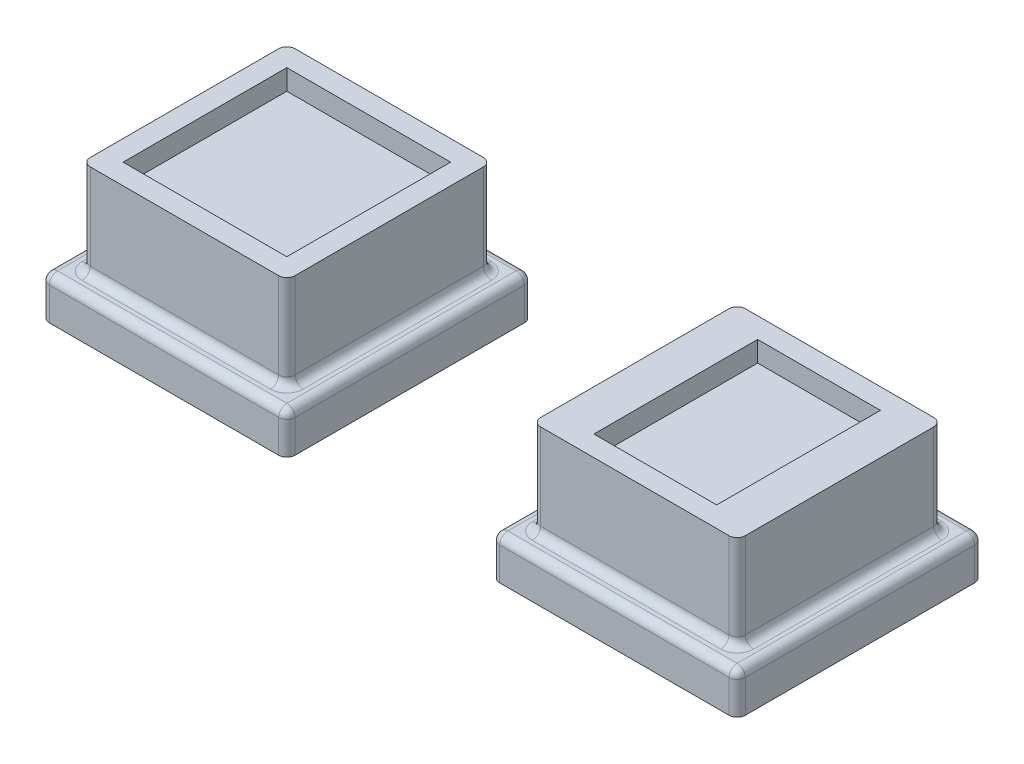
SolidWorks part; units mm, degrees
ref_plane "정면" through (0, 0, 0) normal (0, 0, 1) x (1, 0, 0)
ref_plane "윗면" through (0, 0, 0) normal (0, 1, 0) x (1, 0, 0)
ref_plane "우측면" through (0, 0, 0) normal (1, 0, 0) x (0, 0, -1)
sketch "스케치1" plane through (0, 0, 0) normal (0, 1, 0) x (1, 0, 0)
  line L0 (-150.7679, 0) -> (156.4935, 0) construction
  line L1 (0, 85.3477) -> (0, -87.1689) construction
  line L7 (-25, -30) -> (-85, -30)
  line L8 (-25, -30) -> (-25, 30)
  line L9 (-25, 30) -> (-85, 30)
  line L10 (-85, -30) -> (-85, 30)
  line L11 (-25, -30) -> (-85, 30) construction
  line L12 (-25, 30) -> (-85, -30) construction
  line L13 (85, -30) -> (25, -30)
  line L14 (85, -30) -> (85, 30)
  line L15 (85, 30) -> (25, 30)
  line L16 (25, -30) -> (25, 30)
  line L17 (85, -30) -> (25, 30) construction
  line L18 (85, 30) -> (25, -30) construction
  point P5 (55, 0)
  point P6 (-55, 0)
  dimension "D1" = 25
  dimension "D2" = 25
  dimension "D3" = 60
  dimension "D4" = 60
  dimension "D5" = 60
  dimension "D6" = 60
extrude "보스-돌출1" add sketch "스케치1" along normal blind 10
sketch "스케치4" plane through (0, 10, 0) normal (0, 1, 0) x (1, 0, 0)
  line L0 (-155.3338, 0) -> (146.9333, 0) construction
  line L1 (0, 74.3067) -> (0, -74.7649) construction
  line L3 (-30, -25) -> (-80, -25)
  line L4 (-30, -25) -> (-30, 25)
  line L5 (-30, 25) -> (-80, 25)
  line L6 (-80, -25) -> (-80, 25)
  line L7 (-30, -25) -> (-80, 25) construction
  line L8 (-30, 25) -> (-80, -25) construction
  line L9 (80, -25) -> (30, -25)
  line L10 (80, -25) -> (80, 25)
  line L11 (80, 25) -> (30, 25)
  line L12 (30, -25) -> (30, 25)
  line L13 (80, -25) -> (30, 25) construction
  line L14 (80, 25) -> (30, -25) construction
  point P5 (-55, 0)
  point P10 (55, 0)
  dimension "D1" = 30
  dimension "D2" = 30
  dimension "D3" = 50
  dimension "D4" = 50
  dimension "D5" = 50
  dimension "D6" = 50
extrude "보스-돌출3" add sketch "스케치4" along normal blind 23
fillet "필렛6" radius 2 16 edges at (-55, 10, -30) (-25, 10, 0) (-55, 10, 30) (-85, 10, 0) (-55, 10, 25) (-30, 10, 0) (-55, 10, -25) (-80, 10, 0) (-30, 21.5, -25) (-80, 21.5, -25) (-80, 21.5, 25) (-30, 21.5, 25) (-85, 5, -30) (-25, 5, -30) (-25, 5, 30) (-85, 5, 30)
fillet "필렛7" radius 2 12 edges at (55, 10, -30) (85, 10, 0) (55, 10, 30) (25, 10, 0) (30, 21.5, 25) (30, 21.5, -25) (80, 21.5, -25) (80, 21.5, 25) (25, 5, -30) (85, 5, -30) (85, 5, 30) (25, 5, 30)
sketch "스케치5" plane through (0, 33, 0) normal (0, 1, 0) x (1, 0, 0)
  line L0 (-131.5068, 0) -> (-16.1902, 0) construction
  line L1 (-55, 59.6439) -> (-55, -64.5315) construction
  line L4 (-80, 23) -> (-80, -23) construction
  line L5 (-35, -20) -> (-75, -20)
  line L6 (-35, -20) -> (-35, 20)
  line L7 (-35, 20) -> (-75, 20)
  line L8 (-75, -20) -> (-75, 20)
  line L9 (-35, -20) -> (-75, 20) construction
  line L10 (-35, 20) -> (-75, -20) construction
  point P7 (-55, 0)
  dimension "D1" = 40
  dimension "D2" = 5
  dimension "D3" = 40
extrude "컷-돌출1" cut sketch "스케치5" against normal blind 5
sketch "스케치6" plane through (0, 33, 0) normal (0, 1, 0) x (1, 0, 0)
  line L0 (18.9394, 0) -> (157.1667, 0) construction
  line L1 (55, 48.0359) -> (55, -54.1454) construction
  line L2 (30, 23) -> (30, -23) construction
  line L4 (70, -20) -> (40, -20)
  line L5 (70, -20) -> (70, 20)
  line L6 (70, 20) -> (40, 20)
  line L7 (40, -20) -> (40, 20)
  line L8 (70, -20) -> (40, 20) construction
  line L9 (70, 20) -> (40, -20) construction
  point P7 (55, 0)
  dimension "D1" = 25
  dimension "D2" = 30
  dimension "D3" = 40
extrude "컷-돌출2" cut sketch "스케치6" against normal blind 5
fillet "필렛8" radius 2 8 edges at (30.5858, 10, 24.4142) (30, 10, 0) (30.5858, 10, -24.4142) (55, 10, -25) (79.4142, 10, -24.4142) (80, 10, 0) (79.4142, 10, 24.4142) (55, 10, 25)
